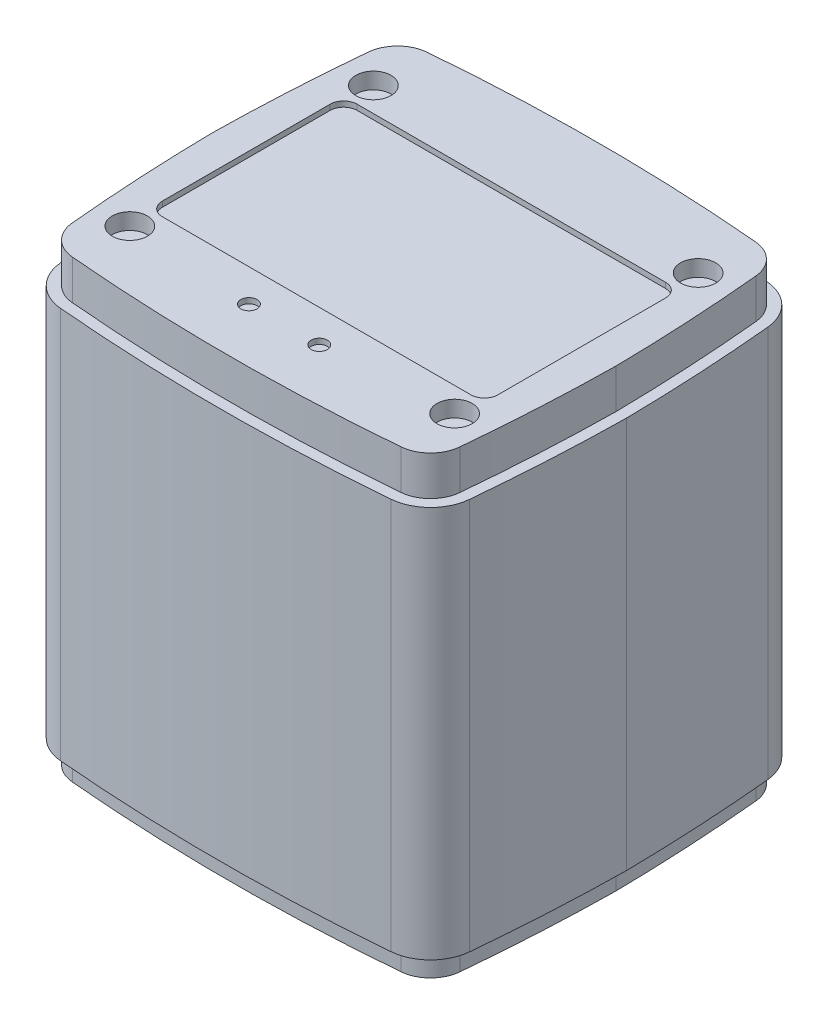
SolidWorks part; units mm, degrees
ref_plane "Front Plane" through (0, 0, 0) normal (0, 0, 1) x (1, 0, 0)
ref_plane "Top Plane" through (0, 0, 0) normal (0, 1, 0) x (1, 0, 0)
ref_plane "Right Plane" through (0, 0, 0) normal (1, 0, 0) x (0, 0, -1)
sketch "Sketch1" plane through (0, 0, 0) normal (0, 1, 0) x (1, 0, 0)
  line L0 (0, 36.1) -> (344.8277, 36.1) construction
  line L1 (0, 0) -> (1.4301, 0)
  line L7 (0, 36.1) -> (340, 31.4905) construction
  line L8 (39.3, 72.2) -> (39.3, 19.9537) construction
  arc A2 (1.4932, 63.6522) -> (0, 36.1) centre (340, 31.4905) ccw
  arc A3 (69.8408, 70.865) -> (8.7592, 70.865) centre (39.3, -277.8) ccw
  arc A4 (77.1068, 63.6522) -> (78.6, 36.1) centre (-261.4, 31.4905) cw
  arc A5 (1.4932, 8.5478) -> (0, 36.1) centre (340, 40.7095) cw
  arc A6 (69.8408, 1.335) -> (8.7592, 1.335) centre (39.3, 350) cw
  arc A7 (77.1068, 8.5478) -> (78.6, 36.1) centre (-261.4, 40.7095) ccw
  arc A8 (1.4932, 8.5478) -> (8.7592, 1.335) centre (9.4573, 9.3045) ccw
  arc A9 (69.8408, 1.335) -> (77.1068, 8.5478) centre (69.1427, 9.3045) ccw
  arc A10 (77.1068, 63.6522) -> (69.8408, 70.865) centre (69.1427, 62.8955) ccw
  arc A11 (8.7592, 70.865) -> (1.4932, 63.6522) centre (9.4573, 62.8955) ccw
  point P19 (2.1823, 1.9737)
  point P23 (76.4177, 1.9737)
  point P26 (76.4177, 70.2263)
  point P29 (2.1823, 70.2263)
  dimension "D3" = 340.0312
  dimension "D4" = 350
  dimension "D6" = 8
  dimension "D1" = 39.3
  dimension "D2" = 36.1
  dimension "D5" = 70.2263
  dimension "D7" = 34.1527
  dimension "D8" = 313.9
extrude "Boss-Extrude1" add sketch "Sketch1" along normal blind 72.4 contours A3 A11 A2 A5 A8 A6 A9 A7 A4 A10
sketch "Sketch2" plane through (0, 72.4, 0) normal (0, 1, 0) x (1, 0, 0)
  arc A0 (69.6663, 68.8726) -> (8.9337, 68.8726) centre (39.3, -277.8) ccw
  arc A1 (8.9337, 68.8726) -> (3.4842, 63.463) centre (9.4573, 62.8955) ccw
  arc A2 (3.4842, 63.463) -> (2.0002, 36.1) centre (340, 31.4905) ccw
  arc A3 (2.0002, 36.1) -> (3.4842, 8.737) centre (340, 40.7095) ccw
  arc A4 (3.4842, 8.737) -> (8.9337, 3.3274) centre (9.4573, 9.3045) ccw
  arc A5 (8.9337, 3.3274) -> (69.6663, 3.3274) centre (39.3, 350) ccw
  arc A6 (69.6663, 3.3274) -> (75.1158, 8.737) centre (69.1427, 9.3045) ccw
  arc A7 (75.1158, 8.737) -> (76.5998, 36.1) centre (-261.4, 40.7095) ccw
  arc A8 (76.5998, 36.1) -> (75.1158, 63.463) centre (-261.4, 31.4905) ccw
  arc A9 (75.1158, 63.463) -> (69.6663, 68.8726) centre (69.1427, 62.8955) ccw
  arc A10 (69.8408, 70.865) -> (8.7592, 70.865) centre (39.3, -277.8) ccw
  arc A11 (8.7592, 70.865) -> (1.4932, 63.6522) centre (9.4573, 62.8955) ccw
  arc A12 (1.4932, 63.6522) -> (0, 36.1) centre (340, 31.4905) ccw
  arc A13 (0, 36.1) -> (1.4932, 8.5478) centre (340, 40.7095) ccw
  arc A14 (1.4932, 8.5478) -> (8.7592, 1.335) centre (9.4573, 9.3045) ccw
  arc A15 (8.7592, 1.335) -> (69.8408, 1.335) centre (39.3, 350) ccw
  arc A16 (69.8408, 1.335) -> (77.1068, 8.5478) centre (69.1427, 9.3045) ccw
  arc A17 (77.1068, 8.5478) -> (78.6, 36.1) centre (-261.4, 40.7095) ccw
  arc A18 (78.6, 36.1) -> (77.1068, 63.6522) centre (-261.4, 31.4905) ccw
  arc A19 (77.1068, 63.6522) -> (69.8408, 70.865) centre (69.1427, 62.8955) ccw
  arc A20 (69.8408, 70.865) -> (8.7592, 70.865) centre (39.3, -277.8) ccw
  arc A21 (8.7592, 70.865) -> (1.4932, 63.6522) centre (9.4573, 62.8955) ccw
  arc A22 (1.4932, 63.6522) -> (0, 36.1) centre (340, 31.4905) ccw
  arc A23 (0, 36.1) -> (1.4932, 8.5478) centre (340, 40.7095) ccw
  arc A24 (1.4932, 8.5478) -> (8.7592, 1.335) centre (9.4573, 9.3045) ccw
  arc A25 (8.7592, 1.335) -> (69.8408, 1.335) centre (39.3, 350) ccw
  arc A26 (69.8408, 1.335) -> (77.1068, 8.5478) centre (69.1427, 9.3045) ccw
  arc A27 (77.1068, 8.5478) -> (78.6, 36.1) centre (-261.4, 40.7095) ccw
  arc A28 (78.6, 36.1) -> (77.1068, 63.6522) centre (-261.4, 31.4905) ccw
  arc A29 (77.1068, 63.6522) -> (69.8408, 70.865) centre (69.1427, 62.8955) ccw
  dimension "D1" = 0
  dimension "D2" = 2
extrude "Boss-Extrude2" add sketch "Sketch2" along normal blind 7.3 contours A0 A1 A2 A3 A4 A5 A6 A7 A8 A9
sketch "Sketch3" plane through (0, 0, 0) normal (0, -1, 0) x (1, 0, 0)
  arc A0 (69.6663, -3.3274) -> (8.9337, -3.3274) centre (39.3, -350) ccw
  arc A1 (8.9337, -3.3274) -> (3.4842, -8.737) centre (9.4573, -9.3045) ccw
  arc A2 (3.4842, -8.737) -> (2.0002, -36.1) centre (340, -40.7095) ccw
  arc A3 (2.0002, -36.1) -> (3.4842, -63.463) centre (340, -31.4905) ccw
  arc A4 (3.4842, -63.463) -> (8.9337, -68.8726) centre (9.4573, -62.8955) ccw
  arc A5 (8.9337, -68.8726) -> (69.6663, -68.8726) centre (39.3, 277.8) ccw
  arc A6 (69.6663, -68.8726) -> (75.1158, -63.463) centre (69.1427, -62.8955) ccw
  arc A7 (75.1158, -63.463) -> (76.5998, -36.1) centre (-261.4, -31.4905) ccw
  arc A8 (76.5998, -36.1) -> (75.1158, -8.737) centre (-261.4, -40.7095) ccw
  arc A9 (75.1158, -8.737) -> (69.6663, -3.3274) centre (69.1427, -9.3045) ccw
  arc A10 (8.7592, -70.865) -> (69.8408, -70.865) centre (39.3, 277.8) ccw
  arc A11 (69.8408, -70.865) -> (77.1068, -63.6522) centre (69.1427, -62.8955) ccw
  arc A12 (77.1068, -63.6522) -> (78.6, -36.1) centre (-261.4, -31.4905) ccw
  arc A13 (78.6, -36.1) -> (77.1068, -8.5478) centre (-261.4, -40.7095) ccw
  arc A14 (77.1068, -8.5478) -> (69.8408, -1.335) centre (69.1427, -9.3045) ccw
  arc A15 (69.8408, -1.335) -> (8.7592, -1.335) centre (39.3, -350) ccw
  arc A16 (8.7592, -1.335) -> (1.4932, -8.5478) centre (9.4573, -9.3045) ccw
  arc A17 (1.4932, -8.5478) -> (0, -36.1) centre (340, -40.7095) ccw
  arc A18 (0, -36.1) -> (1.4932, -63.6522) centre (340, -31.4905) ccw
  arc A19 (1.4932, -63.6522) -> (8.7592, -70.865) centre (9.4573, -62.8955) ccw
  arc A20 (8.7592, -70.865) -> (69.8408, -70.865) centre (39.3, 277.8) ccw
  arc A21 (69.8408, -70.865) -> (77.1068, -63.6522) centre (69.1427, -62.8955) ccw
  arc A22 (77.1068, -63.6522) -> (78.6, -36.1) centre (-261.4, -31.4905) ccw
  arc A23 (78.6, -36.1) -> (77.1068, -8.5478) centre (-261.4, -40.7095) ccw
  arc A24 (77.1068, -8.5478) -> (69.8408, -1.335) centre (69.1427, -9.3045) ccw
  arc A25 (69.8408, -1.335) -> (8.7592, -1.335) centre (39.3, -350) ccw
  arc A26 (8.7592, -1.335) -> (1.4932, -8.5478) centre (9.4573, -9.3045) ccw
  arc A27 (1.4932, -8.5478) -> (0, -36.1) centre (340, -40.7095) ccw
  arc A28 (0, -36.1) -> (1.4932, -63.6522) centre (340, -31.4905) ccw
  arc A29 (1.4932, -63.6522) -> (8.7592, -70.865) centre (9.4573, -62.8955) ccw
  dimension "D1" = 0
  dimension "D2" = 2
extrude "Boss-Extrude3" add sketch "Sketch3" along normal blind 4.3 contours A0 A1 A2 A3 A4 A5 A6 A7 A8 A9
sketch "Sketch4" plane through (0, -4.3, 0) normal (0, -1, 0) x (1, 0, 0)
  circle A0 centre (39.3, -36.1) radius 25
  arc A1 (8.7592, -70.865) -> (69.8408, -70.865) centre (39.3, 277.8) ccw construction
  point P6 (39.3, -72.2)
  dimension "D1" = 50
  dimension "D2" = 39.3
  dimension "D3" = 36.1
extrude "Boss-Extrude4" add sketch "Sketch4" along normal blind 6.5
sketch "Sketch5" plane through (0, 79.7, 0) normal (0, 1, 0) x (1, 0, 0)
  line L0 (39.3, 2) -> (39.3, 55.0475) construction
  circle A1 centre (69.3, 58.6) radius 3.25
  circle A3 centre (69.3, 13.6) radius 3.25
  arc A6 (8.9337, 3.3274) -> (69.6663, 3.3274) centre (39.3, 350) ccw construction
  circle A8 centre (9.3, 13.6) radius 3.25
  circle A9 centre (9.3, 58.6) radius 3.25
  dimension "D1" = 30
  dimension "D2" = 6.5
  dimension "D3" = 6.5
  dimension "D4" = 30
  dimension "D8" = 45
  dimension "D9" = 22.5
extrude "Cut-Extrude1" cut sketch "Sketch5" against normal blind 3
sketch "Sketch6" plane through (0, 79.7, 0) normal (0, 1, 0) x (1, 0, 0)
  line L1 (10.8, 54.1) -> (67.8, 54.1)
  line L2 (8.3, 51.6) -> (8.3, 20.6)
  line L3 (10.8, 18.1) -> (67.8, 18.1)
  line L4 (70.3, 51.6) -> (70.3, 20.6)
  arc A0 (8.7592, 1.335) -> (69.8408, 1.335) centre (39.3, 350) ccw construction
  arc A1 (67.8, 54.1) -> (70.3, 51.6) centre (67.8, 51.6) cw
  arc A2 (67.8, 18.1) -> (70.3, 20.6) centre (67.8, 20.6) ccw
  arc A3 (8.3, 20.6) -> (10.8, 18.1) centre (10.8, 20.6) ccw
  arc A4 (10.8, 54.1) -> (8.3, 51.6) centre (10.8, 51.6) ccw
  point P8 (39.3, 0)
  point P12 (70.3, 54.1)
  point P17 (8.3, 18.1)
  point P20 (8.3, 54.1)
  dimension "D5" = 2.5
  dimension "D1" = 62
  dimension "D2" = 36
  dimension "D3" = 31
  dimension "D4" = 18
extrude "Cut-Extrude2" cut sketch "Sketch6" against normal blind 1
sketch "Sketch7" plane through (0, 79.7, 0) normal (0, 1, 0) x (1, 0, 0)
  line L0 (10.8, 18.1) -> (67.8, 18.1) construction
  line L1 (10.8, 18.1) -> (67.8, 18.1) construction
  circle A0 centre (32.8, 12.1) radius 1.5
  circle A1 centre (45.8, 12.1) radius 1.5
  point P6 (39.3, 18.1)
  dimension "D1" = 3
  dimension "D2" = 3
  dimension "D3" = 13
  dimension "D4" = 6
  dimension "D5" = 6.5
  dimension "D6" = 6
extrude "Cut-Extrude3" cut sketch "Sketch7" against normal blind 1
sketch "Sketch8" plane through (0, -10.8, 0) normal (0, -1, 0) x (1, 0, 0)
  circle A0 centre (39.3, -36.1) radius 20
  dimension "D1" = 40
extrude "Cut-Extrude4" cut sketch "Sketch8" against normal blind 10
